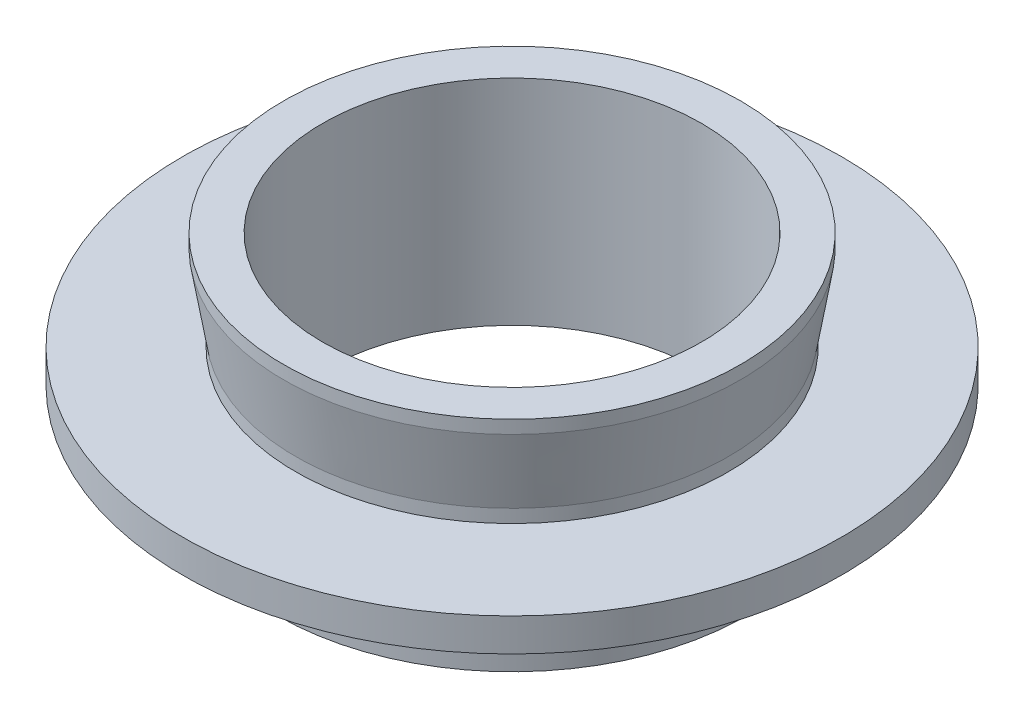
SolidWorks part; units mm, degrees
ref_plane "前视基准面" through (0, 0, 0) normal (0, 0, 1) x (1, 0, 0)
ref_plane "上视基准面" through (0, 0, 0) normal (0, 1, 0) x (1, 0, 0)
ref_plane "右视基准面" through (0, 0, 0) normal (1, 0, 0) x (0, 0, -1)
sketch "草图1" plane through (0, 0, 0) normal (0, 0, 1) x (1, 0, 0)
  line L0 (0, 0) -> (0, 73.2965) construction
  line L1 (-11.5, 0) -> (-11.5, 13)
  line L2 (-11.5, 13) -> (-13.865, 13)
  line L3 (-13.865, 13) -> (-13.865, 12.2)
  line L4 (-13.865, 12.2) -> (-13.135, 7.8)
  line L5 (-13.135, 7.8) -> (-13.135, 7)
  line L6 (-13.135, 7) -> (-20, 7)
  line L7 (-20, 7) -> (-20, 5)
  line L8 (-20, 5) -> (-14, 5)
  line L9 (-14, 5) -> (-14, 4)
  line L10 (-14, 4) -> (-14.25, 4)
  line L11 (-14.25, 4) -> (-14.25, 0)
  line L12 (-14.25, 0) -> (-11.5, 0)
  dimension "D1" = 11.5
  dimension "D2" = 13.865
  dimension "D3" = 13.135
  dimension "D4" = 14.25
  dimension "D5" = 14
  dimension "D6" = 13
  dimension "D7" = 6
  dimension "D8" = 2
  dimension "D9" = 1
  dimension "D10" = 0.8
  dimension "D11" = 0.8
  dimension "D12" = 0
  dimension "D13" = 20
revolve "旋转1" add sketch "草图1" angle 360 about L0
cosmetic thread "装饰螺纹线1" parameters "D1"=13, "D2"=24
cosmetic thread "装饰螺纹线2" parameters "D2"=27.5
